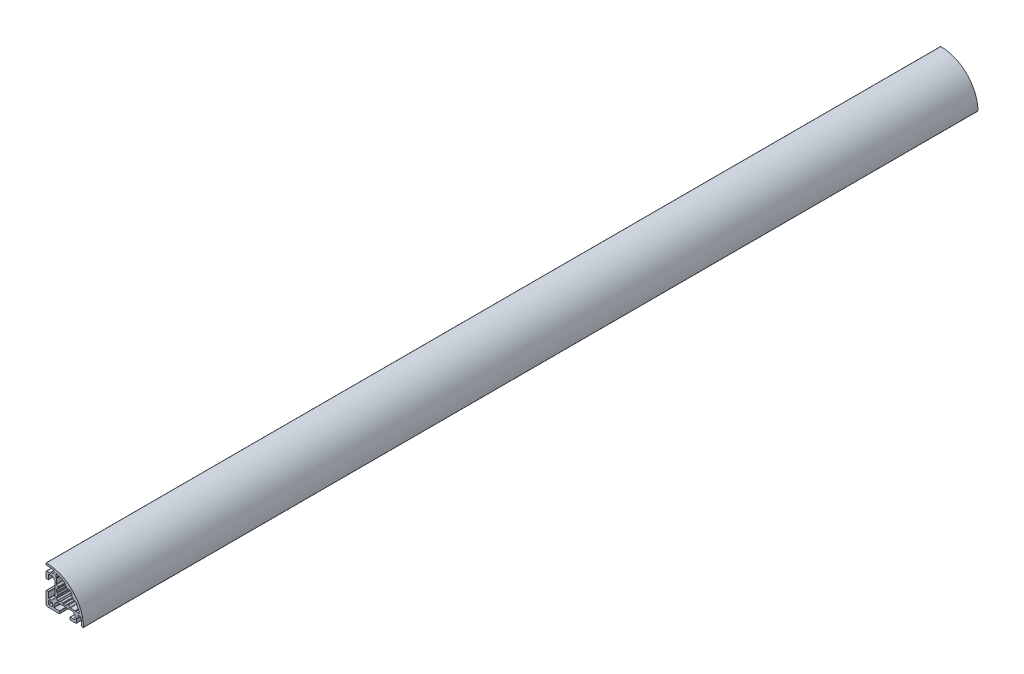
SolidWorks part; units mm, degrees
ref_plane "Plano frontal" through (0, 0, 0) normal (0, 0, 1) x (1, 0, 0)
ref_plane "Plano superior" through (0, 0, 0) normal (0, 1, 0) x (1, 0, 0)
ref_plane "Plano direito" through (0, 0, 0) normal (1, 0, 0) x (0, 0, -1)
ref_plane "Plano1" through (0, 0, 0) normal (0, 0, -1) x (-1, 0, 0)
sketch "Esboço1" plane through (0, 0, 0) normal (0, 0, -1) x (-1, 0, 0)
  line L0 (12.7, -13) -> (10.3, -13)
  line L1 (10, -12.7) -> (10, -10.3)
  line L2 (10.3, -10) -> (12.7, -10)
  line L3 (13, -10.3) -> (13, -12.7)
  line L4 (-0.95, 6.7) -> (-0.3, 6.7)
  line L5 (0, 7) -> (0, 8.4776)
  line L6 (7, 11.4273) -> (7, 8.6799)
  line L7 (6.9121, 8.4678) -> (6.7879, 8.3435)
  line L8 (6.7, 8.1314) -> (6.7, 4.3494)
  line L9 (6.6121, 4.1372) -> (5.4871, 3.0123)
  line L10 (6.1579, 1.25) -> (6.4, 1.25)
  line L11 (6.7, 0.95) -> (6.7, -0.95)
  line L12 (6.4, -1.25) -> (6.1579, -1.25)
  line L13 (5.4871, -3.0123) -> (6.6121, -4.1372)
  line L14 (6.7, -4.3494) -> (6.7, -5.4396)
  line L15 (6.6121, -5.6517) -> (5.6517, -6.6121)
  line L16 (5.4395, -6.7) -> (4.3494, -6.7)
  line L17 (4.1373, -6.6121) -> (3.0123, -5.4871)
  line L18 (1.25, -6.1579) -> (1.25, -6.4)
  line L19 (0.95, -6.7) -> (-0.95, -6.7)
  line L20 (-1.25, -6.4) -> (-1.25, -6.1579)
  line L21 (-3.0123, -5.4871) -> (-4.1373, -6.6121)
  line L22 (-4.3494, -6.7) -> (-8.1314, -6.7)
  line L23 (-8.3435, -6.7879) -> (-8.4678, -6.9121)
  line L24 (-8.6799, -7) -> (-11.4273, -7)
  line L25 (-8.4777, 0) -> (-7, 0)
  line L26 (-6.7, 0.3) -> (-6.7, 0.95)
  line L27 (-6.4, 1.25) -> (-6.1579, 1.25)
  line L28 (-5.4871, 3.0123) -> (-5.7974, 3.3226)
  line L29 (-3.3226, 5.7974) -> (-3.0123, 5.4871)
  line L30 (-1.25, 6.1579) -> (-1.25, 6.4)
  line L31 (7.9882, 6.4323) -> (8.7045, 7.0724)
  line L32 (8.7045, 7.0724) -> (8.7283, 7.4961)
  line L33 (8.7283, 7.4961) -> (9.1516, 7.4723)
  line L34 (9.1516, 7.4723) -> (9.8678, 8.1124)
  line L35 (10.08, 8.2002) -> (12.7001, 8.2002)
  line L36 (13.0001, 7.9002) -> (13, 4.3502)
  line L37 (13.3, 4.0502) -> (14.7, 4.0502)
  line L38 (15, 4.3502) -> (15, 8.8999)
  line L39 (14.5, 9.3999) -> (11.3, 9.3999)
  line L40 (11, 9.6999) -> (11, 10.1999)
  line L41 (10.7, 10.4999) -> (8.8, 10.4999)
  line L42 (8.5, 10.7999) -> (8.5, 12.51)
  line L43 (15, 13.7984) -> (15, 14.6985)
  line L44 (-14.6985, -15) -> (-13.7984, -15)
  line L45 (-12.5105, -8.5) -> (-10.8005, -8.5)
  line L46 (-10.5005, -8.8) -> (-10.5005, -10.7)
  line L47 (-10.2005, -11) -> (-9.7004, -11)
  line L48 (-9.4004, -11.3) -> (-9.4004, -14.5)
  line L49 (-8.9004, -15) -> (-4.3505, -15)
  line L50 (-4.0505, -14.7) -> (-4.0504, -13.3)
  line L51 (-4.3504, -13) -> (-7.9005, -12.9999)
  line L52 (-8.2005, -12.6999) -> (-8.2004, -10.0799)
  line L53 (-8.1126, -9.8677) -> (-7.4725, -9.1515)
  line L54 (-7.4725, -9.1515) -> (-7.4963, -8.728)
  line L55 (-7.4963, -8.728) -> (-7.0727, -8.7042)
  line L56 (-7.0727, -8.7042) -> (-6.4326, -7.988)
  line L57 (-6.2205, -7.9001) -> (6.2197, -7.9001)
  line L58 (6.4318, -7.988) -> (8.7117, -10.4679)
  line L59 (8.7996, -10.6801) -> (8.7996, -12.7001)
  line L60 (8.4996, -13.0001) -> (4.3496, -13.0001)
  line L61 (4.0496, -13.3001) -> (4.0496, -14.7)
  line L62 (4.3496, -15) -> (13.5, -15)
  line L63 (15, -13.5) -> (15, -4.35)
  line L64 (14.7, -4.05) -> (13.2999, -4.05)
  line L65 (12.9999, -4.35) -> (12.9999, -8.4999)
  line L66 (12.6999, -8.7999) -> (10.6798, -8.7999)
  line L67 (10.4677, -8.712) -> (7.9878, -6.4321)
  line L68 (7.9003, -6.22) -> (7.9003, 6.2202)
  arc A0 (10.3, -13) -> (10, -12.7) centre (10.3, -12.7) cw
  arc A1 (10, -10.3) -> (10.3, -10) centre (10.3, -10.3) cw
  arc A2 (12.7, -10) -> (13, -10.3) centre (12.7, -10.3) cw
  arc A3 (13, -12.7) -> (12.7, -13) centre (12.7, -12.7) cw
  arc A4 (-0.3, 6.7) -> (0, 7) centre (-0.3, 7) ccw
  arc A5 (0, 8.4776) -> (0.1408, 8.7319) centre (0.3, 8.4776) cw
  arc A6 (0.1408, 8.7319) -> (6.6101, 11.7135) centre (15, -15) cw
  arc A7 (6.6101, 11.7135) -> (7, 11.4273) centre (6.7, 11.4273) cw
  arc A8 (7, 8.6799) -> (6.9121, 8.4678) centre (6.7, 8.6799) cw
  arc A9 (6.7879, 8.3435) -> (6.7, 8.1314) centre (7, 8.1314) ccw
  arc A10 (6.7, 4.3494) -> (6.6121, 4.1372) centre (6.4, 4.3494) cw
  arc A11 (5.4871, 3.0123) -> (5.43, 2.6678) centre (5.6993, 2.8001) ccw
  arc A12 (5.43, 2.6678) -> (5.867, 1.4768) centre (0, 0) cw
  arc A13 (5.867, 1.4768) -> (6.1579, 1.25) centre (6.1579, 1.55) ccw
  arc A14 (6.4, 1.25) -> (6.7, 0.95) centre (6.4, 0.95) cw
  arc A15 (6.7, -0.95) -> (6.4, -1.25) centre (6.4, -0.95) cw
  arc A16 (6.1579, -1.25) -> (5.867, -1.4768) centre (6.1579, -1.55) ccw
  arc A17 (5.867, -1.4768) -> (5.43, -2.6678) centre (0, 0) cw
  arc A18 (5.43, -2.6678) -> (5.4871, -3.0123) centre (5.6993, -2.8001) ccw
  arc A19 (6.6121, -4.1372) -> (6.7, -4.3494) centre (6.4, -4.3494) cw
  arc A20 (6.7, -5.4396) -> (6.6121, -5.6517) centre (6.4, -5.4396) cw
  arc A21 (5.6517, -6.6121) -> (5.4395, -6.7) centre (5.4395, -6.4) cw
  arc A22 (4.3494, -6.7) -> (4.1373, -6.6121) centre (4.3494, -6.4) cw
  arc A23 (3.0123, -5.4871) -> (2.6678, -5.43) centre (2.8001, -5.6993) ccw
  arc A24 (2.6678, -5.43) -> (1.4768, -5.867) centre (0, 0) cw
  arc A25 (1.4768, -5.867) -> (1.25, -6.1579) centre (1.55, -6.1579) ccw
  arc A26 (1.25, -6.4) -> (0.95, -6.7) centre (0.95, -6.4) cw
  arc A27 (-0.95, -6.7) -> (-1.25, -6.4) centre (-0.95, -6.4) cw
  arc A28 (-1.25, -6.1579) -> (-1.4768, -5.867) centre (-1.55, -6.1579) ccw
  arc A29 (-1.4768, -5.867) -> (-2.6678, -5.43) centre (0, 0) cw
  arc A30 (-2.6678, -5.43) -> (-3.0123, -5.4871) centre (-2.8001, -5.6993) ccw
  arc A31 (-4.1373, -6.6121) -> (-4.3494, -6.7) centre (-4.3494, -6.4) cw
  arc A32 (-8.1314, -6.7) -> (-8.3435, -6.7879) centre (-8.1314, -7) ccw
  arc A33 (-8.4678, -6.9121) -> (-8.6799, -7) centre (-8.6799, -6.7) cw
  arc A34 (-11.4273, -7) -> (-11.7135, -6.6101) centre (-11.4273, -6.7) cw
  arc A35 (-11.7135, -6.6101) -> (-8.7319, -0.1408) centre (15, -15) cw
  arc A36 (-8.7319, -0.1408) -> (-8.4777, 0) centre (-8.4777, -0.3) cw
  arc A37 (-7, 0) -> (-6.7, 0.3) centre (-7, 0.3) ccw
  arc A38 (-6.7, 0.95) -> (-6.4, 1.25) centre (-6.4, 0.95) cw
  arc A39 (-6.1579, 1.25) -> (-5.867, 1.4768) centre (-6.1579, 1.55) ccw
  arc A40 (-5.867, 1.4768) -> (-5.43, 2.6678) centre (0, 0) cw
  arc A41 (-5.43, 2.6678) -> (-5.4871, 3.0123) centre (-5.6993, 2.8001) ccw
  arc A42 (-5.7974, 3.3226) -> (-5.8083, 3.7354) centre (-5.5853, 3.5347) cw
  arc A43 (-5.8083, 3.7354) -> (-3.7354, 5.8083) centre (15, -15) cw
  arc A44 (-3.7354, 5.8083) -> (-3.3226, 5.7974) centre (-3.5347, 5.5853) cw
  arc A45 (-3.0123, 5.4871) -> (-2.6678, 5.43) centre (-2.8001, 5.6993) ccw
  arc A46 (-2.6678, 5.43) -> (-1.4768, 5.867) centre (0, 0) cw
  arc A47 (-1.4768, 5.867) -> (-1.25, 6.1579) centre (-1.55, 6.1579) ccw
  arc A48 (-1.25, 6.4) -> (-0.95, 6.7) centre (-0.95, 6.4) cw
  arc A49 (9.8678, 8.1124) -> (10.08, 8.2002) centre (10.08, 7.9002) cw
  arc A50 (12.7001, 8.2002) -> (13.0001, 7.9002) centre (12.7001, 7.9002) cw
  arc A51 (13, 4.3502) -> (13.3, 4.0502) centre (13.3, 4.3502) ccw
  arc A52 (14.7, 4.0502) -> (15, 4.3502) centre (14.7, 4.3502) ccw
  arc A53 (15, 8.8999) -> (14.5, 9.3999) centre (14.5, 8.8999) ccw
  arc A54 (11.3, 9.3999) -> (11, 9.6999) centre (11.3, 9.6999) cw
  arc A55 (11, 10.1999) -> (10.7, 10.4999) centre (10.7, 10.1999) ccw
  arc A56 (8.8, 10.4999) -> (8.5, 10.7999) centre (8.8, 10.7999) cw
  arc A57 (8.5, 12.51) -> (8.734, 12.8026) centre (8.8, 12.51) cw
  arc A58 (8.734, 12.8026) -> (14.7031, 13.4984) centre (15, -15) cw
  arc A59 (14.7031, 13.4984) -> (15, 13.7984) centre (14.7, 13.7984) ccw
  arc A60 (15, 14.6985) -> (14.697, 14.9985) centre (14.7, 14.6985) ccw
  arc A61 (14.697, 14.9985) -> (-14.9985, -14.697) centre (15, -15) ccw
  arc A62 (-14.9985, -14.697) -> (-14.6985, -15) centre (-14.6985, -14.7) ccw
  arc A63 (-13.7984, -15) -> (-13.4985, -14.7031) centre (-13.7984, -14.7) ccw
  arc A64 (-13.4985, -14.7031) -> (-12.8027, -8.734) centre (15, -15) cw
  arc A65 (-12.8027, -8.734) -> (-12.5105, -8.5) centre (-12.51, -8.8) cw
  arc A66 (-10.8005, -8.5) -> (-10.5005, -8.8) centre (-10.8005, -8.8) cw
  arc A67 (-10.5005, -10.7) -> (-10.2005, -11) centre (-10.2005, -10.7) ccw
  arc A68 (-9.7004, -11) -> (-9.4004, -11.3) centre (-9.7004, -11.3) cw
  arc A69 (-9.4004, -14.5) -> (-8.9004, -15) centre (-8.9004, -14.5) ccw
  arc A70 (-4.3505, -15) -> (-4.0505, -14.7) centre (-4.3505, -14.7) ccw
  arc A71 (-4.0504, -13.3) -> (-4.3504, -13) centre (-4.3504, -13.3) ccw
  arc A72 (-7.9005, -12.9999) -> (-8.2005, -12.6999) centre (-7.9005, -12.6999) cw
  arc A73 (-8.2004, -10.0799) -> (-8.1126, -9.8677) centre (-7.9004, -10.0799) cw
  arc A74 (-6.4326, -7.988) -> (-6.2205, -7.9001) centre (-6.2205, -8.2001) cw
  arc A75 (6.2197, -7.9001) -> (6.4318, -7.988) centre (6.2197, -8.2001) cw
  arc A76 (8.7117, -10.4679) -> (8.7996, -10.6801) centre (8.4996, -10.6801) cw
  arc A77 (8.7996, -12.7001) -> (8.4996, -13.0001) centre (8.4996, -12.7001) cw
  arc A78 (4.3496, -13.0001) -> (4.0496, -13.3001) centre (4.3496, -13.3001) ccw
  arc A79 (4.0496, -14.7) -> (4.3496, -15) centre (4.3496, -14.7) ccw
  arc A80 (13.5, -15) -> (15, -13.5) centre (13.5, -13.5) ccw
  arc A81 (15, -4.35) -> (14.7, -4.05) centre (14.7, -4.35) ccw
  arc A82 (13.2999, -4.05) -> (12.9999, -4.35) centre (13.2999, -4.35) ccw
  arc A83 (12.9999, -8.4999) -> (12.6999, -8.7999) centre (12.6999, -8.4999) cw
  arc A84 (10.6798, -8.7999) -> (10.4677, -8.712) centre (10.6798, -8.4999) cw
  arc A85 (7.9878, -6.4321) -> (7.9003, -6.22) centre (8.2003, -6.2204) cw
  arc A86 (7.9003, 6.2202) -> (7.9882, 6.4323) centre (8.2003, 6.2202) cw
  dimension "D1" = 1.5
  dimension "D2" = 30
extrude "Ressalto-extrusão1" add sketch "Esboço1" against normal blind 715
